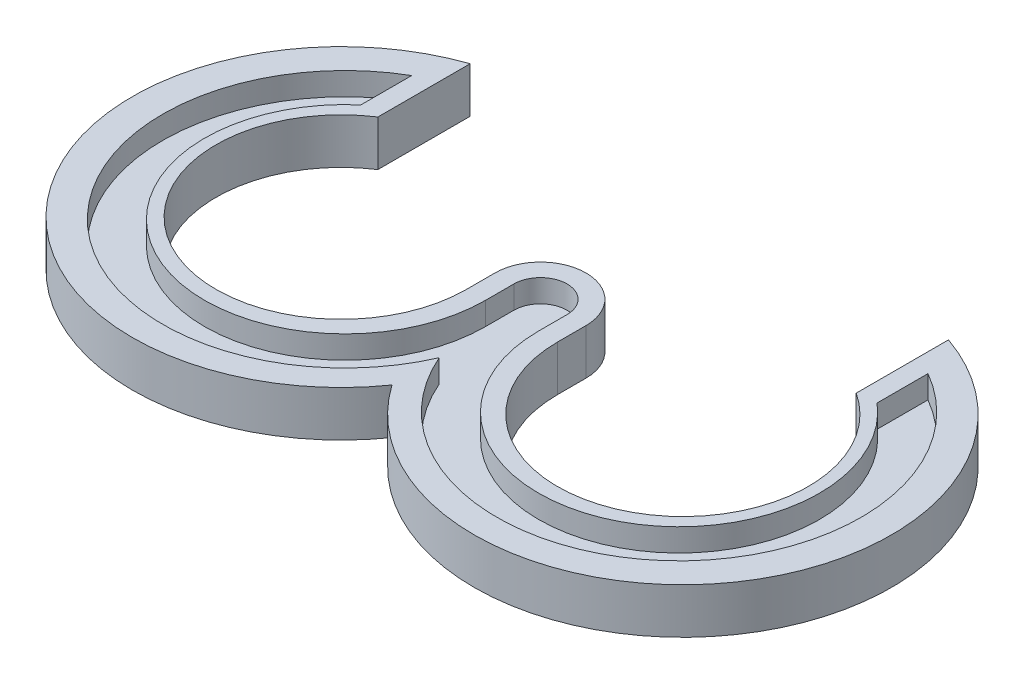
SolidWorks part; units mm, degrees
material "Резина"
ref_plane "Спереди" through (0, 0, 0) normal (0, 0, 1) x (1, 0, 0)
ref_plane "Сверху" through (0, 0, 0) normal (0, 1, 0) x (1, 0, 0)
ref_plane "Справа" through (0, 0, 0) normal (1, 0, 0) x (0, 0, -1)
sketch "Эскиз1" plane through (0, 0, 0) normal (0, 1, 0) x (1, 0, 0)
  line L0 (-6, -3.75) -> (-6, 0)
  line L1 (31.5, 22.2356) -> (31.5, 10.0793)
  line L2 (6, -3.75) -> (6, 0)
  line L3 (-31.5, 22.2356) -> (-31.5, 10.0793)
  line L4 (0, 0) -> (0, 31.6349) construction
  arc A0 (-31.5, 10.0793) -> (-6, -3.75) centre (-22.5, -3.75) ccw
  arc A1 (6, -3.75) -> (31.5, 10.0793) centre (22.5, -3.75) ccw
  arc A2 (-6, 0) -> (6, 0) centre (0, 0) cw
  arc A3 (-31.5, 22.2356) -> (0, -19.5614) centre (-22.5, -3.75) ccw
  arc A4 (0, -19.5614) -> (31.5, 22.2356) centre (22.5, -3.75) ccw
  point P7 (0, 6)
  dimension "D1" = 33
  dimension "D2" = 33
  dimension "D6" = 55
  dimension "D7" = 55
  dimension "D3" = 3.75
  dimension "D4" = 12
  dimension "D5" = 63
extrude "Бобышка-Вытянуть1" add sketch "Эскиз1" along normal blind 6
sketch "Эскиз4" plane through (0, 6, 0) normal (0, 1, 0) x (1, 0, 0)
  line L0 (-3.5, -3.75) -> (-3.5, 0)
  line L1 (34, 17.0346) -> (34, 10.3301)
  line L2 (3.5, -3.75) -> (3.5, 0)
  line L3 (-34, 17.0346) -> (-34, 10.3301)
  line L4 (0, 0) -> (0, 47.1846) construction
  arc A0 (-34, 10.3301) -> (-3.5, -3.75) centre (-22, -3.75) ccw
  arc A1 (3.5, -3.75) -> (34, 10.3301) centre (22, -3.75) ccw
  arc A2 (-3.5, 0) -> (3.5, 0) centre (0, 0) cw
  arc A3 (-34, 17.0346) -> (0, -13.3417) centre (-22, -3.75) ccw
  arc A4 (0, -13.3417) -> (34, 17.0346) centre (22, -3.75) ccw
  point P6 (0, 3.5)
  dimension "D1" = 37
  dimension "D2" = 37
  dimension "D3" = 68
  dimension "D4" = 24
  dimension "D7" = 24
  dimension "D5" = 3.75
  dimension "D6" = 7
extrude "Вырез-Вытянуть1" cut sketch "Эскиз4" against normal blind 3
